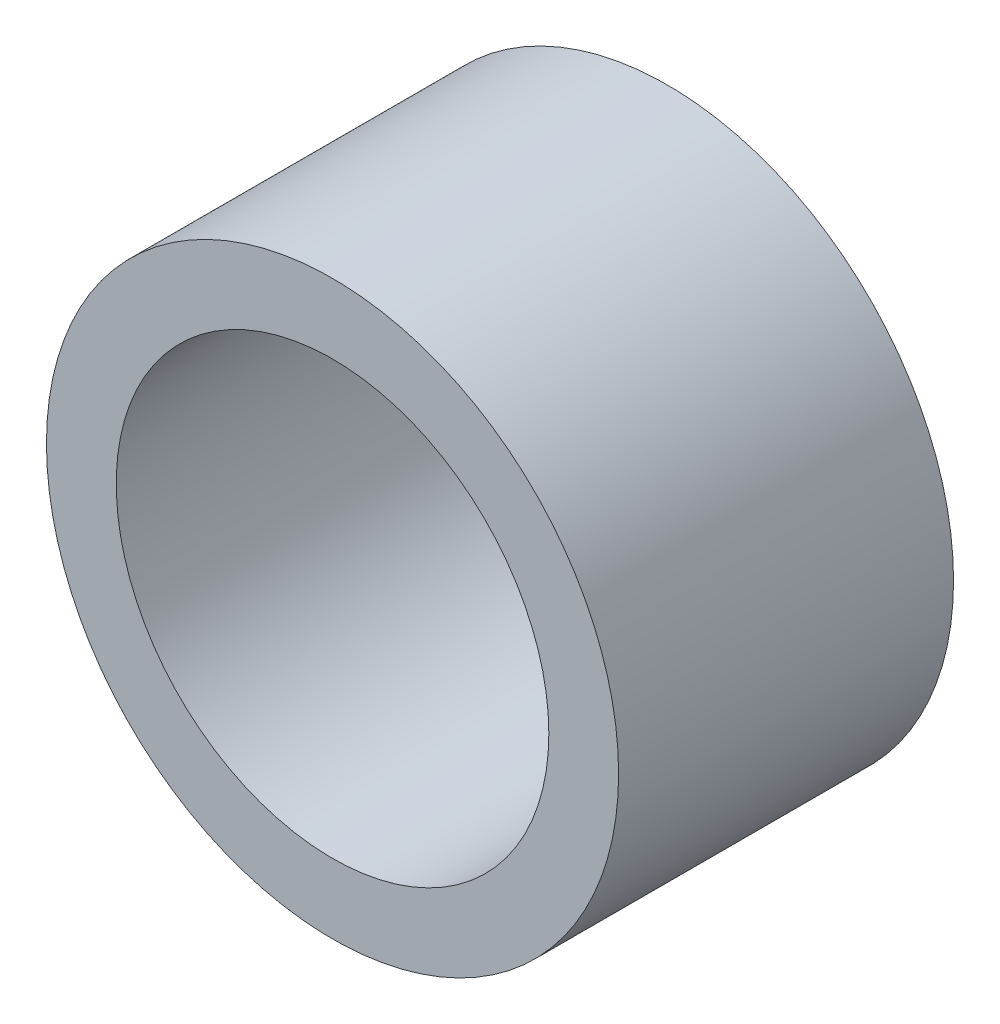
SolidWorks part; units mm, degrees
ref_plane "Front Plane" through (0, 0, 0) normal (0, 0, 1) x (1, 0, 0)
ref_plane "Top Plane" through (0, 0, 0) normal (0, 1, 0) x (1, 0, 0)
ref_plane "Right Plane" through (0, 0, 0) normal (1, 0, 0) x (0, 0, -1)
sketch "Sketch1" plane through (0, 0, 0) normal (0, 0, 1) x (1, 0, 0)
  circle A0 centre (0, 0) radius 3.937
  circle A1 centre (0, 0) radius 5.207
  dimension "D1" = 7.874
  dimension "D2" = 10.414
extrude "Boss-Extrude1" add sketch "Sketch1" along normal blind 6.096
